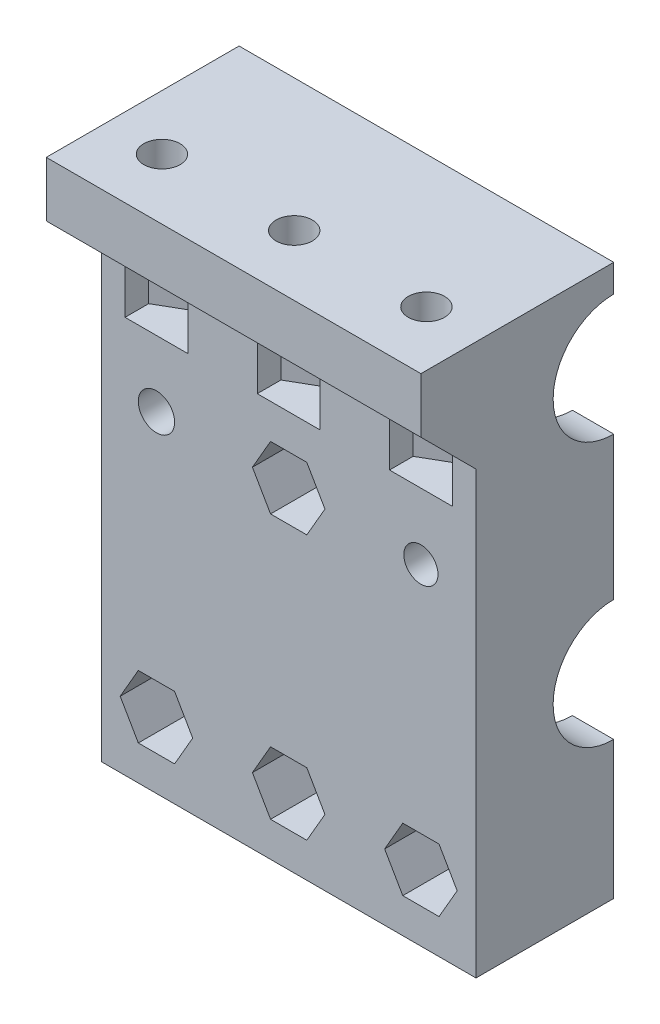
SolidWorks part; units mm, degrees
ref_plane "前视基准面" through (0, 0, 0) normal (0, 0, 1) x (1, 0, 0)
ref_plane "上视基准面" through (0, 0, 0) normal (0, 1, 0) x (1, 0, 0)
ref_plane "右视基准面" through (0, 0, 0) normal (1, 0, 0) x (0, 0, -1)
sketch "草图1" plane through (0, 0, 0) normal (1, 0, 0) x (0, 0, -1)
  line L1 (0, 0) -> (12.5, 0)
  line L2 (0, 0) -> (0, 50)
  line L3 (0, 50) -> (12.5, 50)
  line L4 (12.5, 0) -> (12.5, 50)
  dimension "D1" = 12.5
  dimension "D2" = 50
extrude "凸台-拉伸1" add sketch "草图1" along normal blind 34
ref_plane "基准面1" through (17, 0, 0) normal (-1, 0, 0) x (0, 0, 1)
sketch "草图2" plane through (17, 0, 0) normal (-1, 0, 0) x (0, 0, 1)
  line L0 (-12.5, 0) -> (-12.5, 50) construction
  line L1 (0, 0) -> (-12.5, 0) construction
  circle A0 centre (-12.5, 18) radius 7.5
  circle A1 centre (-12.5, 42) radius 7.5
  dimension "D1" = 15
  dimension "D2" = 15
  dimension "D3" = 18
  dimension "D4" = 24
extrude "切除-拉伸1" cut sketch "草图2" against normal mid plane 26.5
sketch "草图3" plane through (0, 0, 0) normal (0, 0, 1) x (1, 0, 0)
  line L0 (34, 0) -> (34, 50) construction
  line L1 (0, 0) -> (0, 50) construction
  line L2 (34, 0) -> (0, 0) construction
  line L3 (17, 6.875) -> (17, -6.875) construction
  line L4 (34, 0) -> (0, 0) construction
  circle A0 centre (29, 30) radius 1.55
  circle A1 centre (5, 30) radius 1.65
  circle A4 centre (17, 30) radius 1.55
  circle A5 centre (5, 6) radius 1.65
  circle A6 centre (17, 6) radius 1.55
  circle A7 centre (29, 6) radius 1.55
  dimension "D1" = 3.1
  dimension "D2" = 3.3
  dimension "D8" = 3.1
  dimension "D3" = 5
  dimension "D4" = 5
  dimension "D5" = 30
  dimension "D6" = 30
  dimension "D9" = 30
  dimension "D7" = 2
extrude "切除-拉伸2" cut sketch "草图3" against normal through all
sketch "草图4" plane through (0, 0, 0) normal (0, 0, 1) x (1, 0, 0)
  line L0 (34, 0) -> (0, 0) construction
  line L26 (18.6454, 27.15) -> (20.2909, 30)
  line L27 (20.2909, 30) -> (18.6454, 32.85)
  line L28 (18.6454, 32.85) -> (15.3546, 32.85)
  line L29 (15.3546, 32.85) -> (13.7091, 30)
  line L30 (13.7091, 30) -> (15.3546, 27.15)
  line L31 (15.3546, 27.15) -> (18.6454, 27.15)
  line L32 (18.6454, 3.15) -> (20.2909, 6)
  line L33 (20.2909, 6) -> (18.6454, 8.85)
  line L34 (18.6454, 8.85) -> (15.3546, 8.85)
  line L35 (15.3546, 8.85) -> (13.7091, 6)
  line L36 (13.7091, 6) -> (15.3546, 3.15)
  line L37 (15.3546, 3.15) -> (18.6454, 3.15)
  line L39 (30.6454, 3.15) -> (32.2909, 6)
  line L40 (32.2909, 6) -> (30.6454, 8.85)
  line L41 (30.6454, 8.85) -> (27.3546, 8.85)
  line L42 (27.3546, 8.85) -> (25.7091, 6)
  line L43 (25.7091, 6) -> (27.3546, 3.15)
  line L44 (27.3546, 3.15) -> (30.6454, 3.15)
  line L45 (6.6454, 3.15) -> (8.2909, 6)
  line L46 (8.2909, 6) -> (6.6454, 8.85)
  line L47 (6.6454, 8.85) -> (3.3546, 8.85)
  line L48 (3.3546, 8.85) -> (1.7091, 6)
  line L49 (1.7091, 6) -> (3.3546, 3.15)
  line L50 (3.3546, 3.15) -> (6.6454, 3.15)
  circle A0 centre (17, 6) radius 2.85 construction
  circle A2 centre (29, 6) radius 2.85 construction
  circle A3 centre (5, 6) radius 2.85 construction
  circle A4 centre (17, 30) radius 2.85 construction
  dimension "D1" = 2
  dimension "D2" = 2
  dimension "D4" = 5.7
  dimension "D3" = 2
extrude "切除-拉伸3" cut sketch "草图4" against normal blind 5
sketch "草图5" plane through (34, 0, 0) normal (1, 0, 0) x (0, 0, -1)
  line L0 (12.5, 0) -> (12.5, 50) construction
  line L1 (0, 0) -> (12.5, 0) construction
  circle A0 centre (12.5, 18) radius 5.5
  circle A1 centre (12.5, 42) radius 5.5
  dimension "D1" = 11
  dimension "D2" = 11
  dimension "D3" = 18
  dimension "D4" = 24
extrude "切除-拉伸4" cut sketch "草图5" against normal through all
sketch "草图6" plane through (17, 0, 0) normal (-1, 0, 0) x (0, 0, 1)
  line L0 (0, 50) -> (5, 50)
  line L1 (5, 50) -> (5, 45)
  line L2 (5, 45) -> (0, 40)
  line L3 (0, 50) -> (0, 0) construction
  line L4 (0, 40) -> (0, 50)
  dimension "D1" = 5
  dimension "D2" = 10
  dimension "D3" = 45
extrude "凸台-拉伸2" add sketch "草图6" along normal mid plane 34
ref_plane "基准面2" through (0, 45, 0) normal (0, 1, 0) x (1, 0, 0)
sketch "草图7" plane through (0, 45, 0) normal (0, 1, 0) x (1, 0, 0)
  line L0 (5, 12.5) -> (5, 0) construction
  line L1 (17, 9.625) -> (17, -9.625) construction
  line L2 (29, 12.5) -> (29, 0) construction
  line L4 (30.25, 12.5) -> (3.75, 12.5) construction
  circle A0 centre (5, 0.5) radius 1.65
  circle A1 centre (17, 0.5) radius 1.65
  circle A2 centre (29, 0.5) radius 1.65
  dimension "D1" = 3.3
  dimension "D2" = 3.3
  dimension "D3" = 3.3
  dimension "D4" = 12
  dimension "D5" = 12
  dimension "D6" = 12
extrude "切除-拉伸5" cut sketch "草图7" along normal through all
sketch "草图8" plane through (0, 45, 0) normal (0, 1, 0) x (1, 0, 0)
  line L0 (0, 12.5) -> (0, -5) construction
  line L1 (7.85, -0.5908) -> (7.85, 2.1454)
  line L2 (7.85, 2.1454) -> (5, 3.7909)
  line L3 (5, 3.7909) -> (2.15, 2.1454)
  line L4 (2.15, 2.1454) -> (2.15, -0.482)
  line L7 (19.85, -0.5908) -> (19.85, 2.1454)
  line L8 (19.85, 2.1454) -> (17, 3.7909)
  line L9 (17, 3.7909) -> (14.15, 2.1454)
  line L10 (14.15, 2.1454) -> (14.15, -0.482)
  line L13 (31.85, -0.5908) -> (31.85, 2.1454)
  line L14 (31.85, 2.1454) -> (29, 3.7909)
  line L15 (29, 3.7909) -> (26.15, 2.1454)
  line L16 (26.15, 2.1454) -> (26.15, -0.482)
  line L19 (2.15, -0.482) -> (2.15, -5)
  line L20 (0, -5) -> (34, -5) construction
  line L21 (2.15, -5) -> (7.85, -5)
  line L22 (7.85, -5) -> (7.85, -0.5908)
  line L23 (14.15, -0.482) -> (14.15, -5)
  line L24 (14.15, -5) -> (19.85, -5)
  line L25 (19.85, -5) -> (19.85, -0.5908)
  line L26 (26.15, -0.482) -> (26.15, -5)
  line L27 (26.15, -5) -> (31.85, -5)
  line L28 (31.85, -5) -> (31.85, -0.5908)
  line L29 (29.1028, -2.7315) -> (30.5028, -1.9232) [skipped]
  line L30 (26.2528, -1.2048) -> (27.6528, -2.0131) [skipped]
  line L31 (17.1028, -2.7315) -> (18.5028, -1.9232) [skipped]
  line L32 (14.2528, -1.2048) -> (15.6528, -2.0131) [skipped]
  line L33 (6.425, -1.9682) -> (7.825, -1.1599) [skipped]
  line L34 (2.2528, -1.2048) -> (3.6528, -2.0131) [skipped]
  circle A0 centre (5, 0.5) radius 2.85 construction
  circle A1 centre (17, 0.5) radius 2.85 construction
  circle A2 centre (29, 0.5) radius 2.85 construction
  dimension "D1" = 5.7
  dimension "D2" = 5.7
  dimension "D3" = 5.7
extrude "切除-拉伸6" cut sketch "草图8" against normal blind 9
